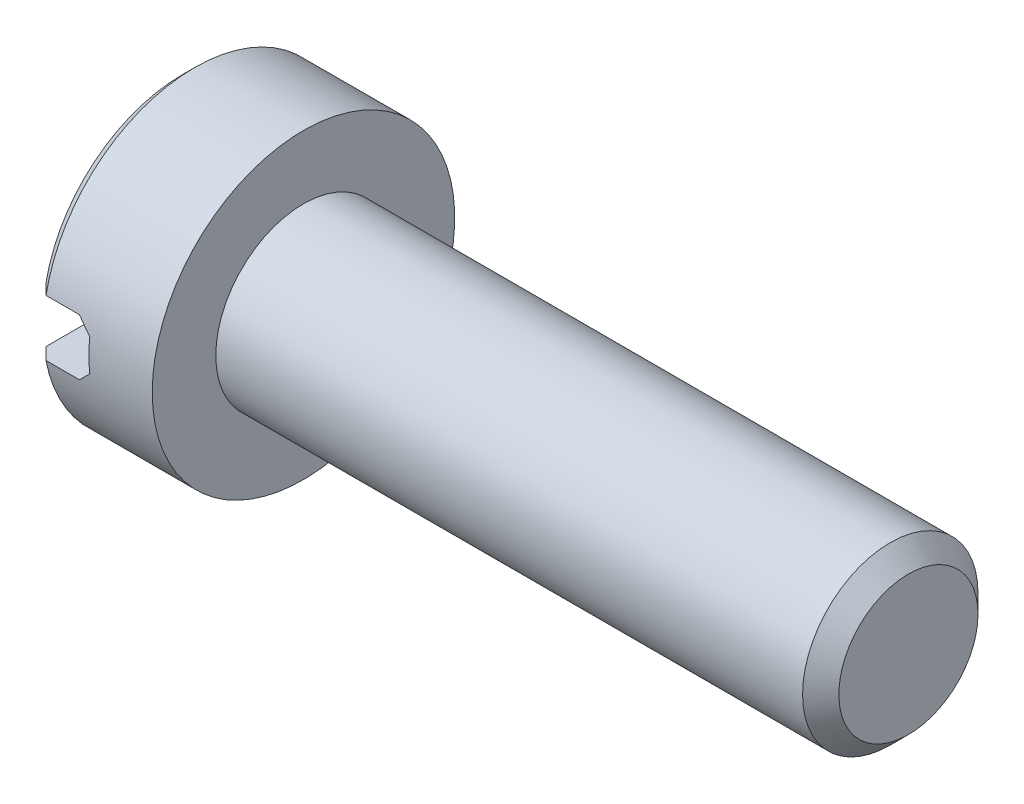
SolidWorks part; units mm, degrees
ref_plane "Face" through (0, 0, 0) normal (0, 0, 1) x (1, 0, 0)
ref_plane "Dessus" through (0, 0, 0) normal (0, 1, 0) x (1, 0, 0)
ref_plane "Droite" through (0, 0, 0) normal (1, 0, 0) x (0, 0, -1)
sketch "Esquisse1" plane through (0, 0, 0) normal (0, 0, 1) x (1, 0, 0)
  line L0 (0, 0) -> (0, 2.3)
  line L1 (0.2, 2.5) -> (2, 2.5)
  line L2 (2, 2.5) -> (2, 0)
  line L5 (0, 0) -> (7.6423, 0) construction
  line L7 (0, 2.3) -> (0.2, 2.5)
  line L8 (0, 0) -> (2, 0)
  point P1 (0, 2.5)
  dimension "D1" = 2.5
  dimension "D3" = 2
  dimension "D9" = 0.2
revolve "Révolution1" add sketch "Esquisse1" angle 360 about L5
sketch "Esquisse2" plane through (0, 0, 0) normal (0, 0, 1) x (1, 0, 0)
  line L0 (0, 2.3) -> (0, -2.3) construction
  line L1 (0, 0.4655) -> (0.7534, 0.4655)
  line L2 (0, 0.4655) -> (0, -0.4655)
  line L3 (0, -0.4655) -> (0.7534, -0.4655)
  line L4 (0.9534, 0.2655) -> (0.9534, -0.2655)
  line L5 (0.7534, 0.4655) -> (0.9534, 0.2655)
  line L6 (0.7534, -0.4655) -> (0.9534, -0.2655)
  point P1 (0.9534, -0.4655)
  point P3 (0.9534, 0.4655)
  dimension "D3" = 0.2
  dimension "D4" = 0.2
extrude "Enlèv. mat.-Extru.1" cut sketch "Esquisse2" against normal mid plane 10
sketch "Esquisse3" plane through (2, 0, 0) normal (1, 0, 0) x (0, 0, -1)
  circle A0 centre (0, 0) radius 1.45
extrude "Extrusion1" add sketch "Esquisse3" along normal blind 10
chamfer "Chanfrein1" distance 0.3 angle 45 1 edges at (12, 0, -1.45)
